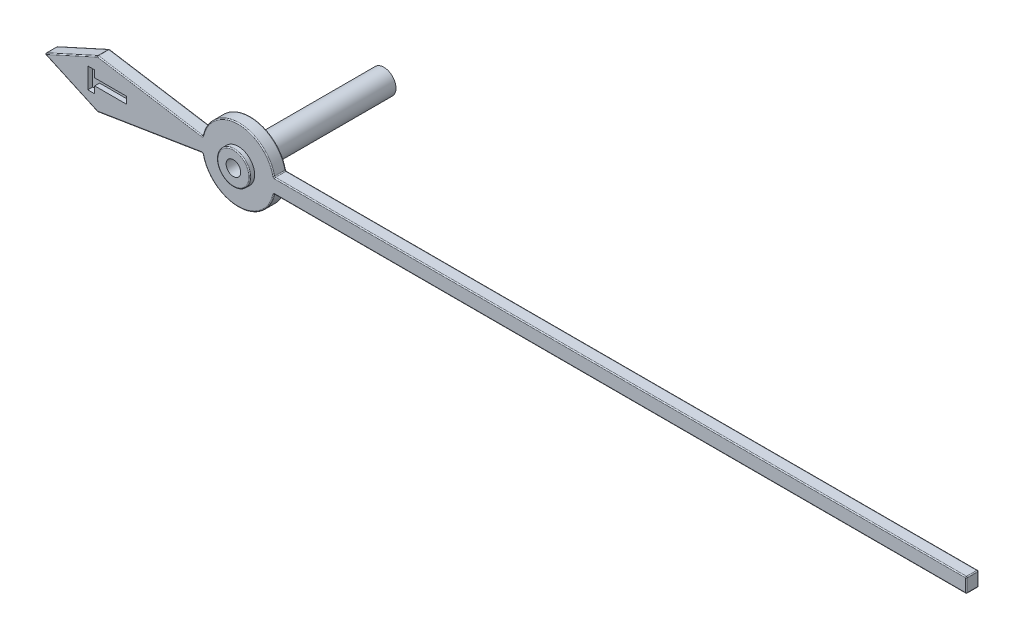
SolidWorks part; units mm, degrees
ref_plane "Front Plane" through (0, 0, 0) normal (0, 0, 1) x (1, 0, 0)
ref_plane "Top Plane" through (0, 0, 0) normal (0, 1, 0) x (1, 0, 0)
ref_plane "Right Plane" through (0, 0, 0) normal (1, 0, 0) x (0, 0, -1)
sketch "Sketch1" plane through (0, 0, 0) normal (0, 0, 1) x (1, 0, 0)
  line L0 (15, 0.15) -> (15, -0.15)
  line L1 (55, 0) -> (-55, 0) construction
  line L2 (0, -55) -> (0, 55) construction
  line L3 (0.7348, -0.15) -> (15, -0.15)
  line L4 (0.7348, 0.15) -> (15, 0.15)
  line L6 (-4, 0) -> (-2.9, 0.5)
  line L7 (-2.9, 0.5) -> (-0.7348, 0.15)
  line L8 (-4, 0) -> (-2.9, -0.5)
  line L9 (-2.9, -0.5) -> (-0.7348, -0.15)
  arc A0 (-0.7348, -0.15) -> (0.7348, -0.15) centre (0, 0) ccw
  circle A1 centre (0, 0) radius 0.25
  arc A2 (0.7348, 0.15) -> (-0.7348, 0.15) centre (0, 0) ccw
  dimension "D3" = 1.5
  dimension "D4" = 0.5
  dimension "D2" = 4
  dimension "D8" = 1
extrude "Boss-Extrude1" add sketch "Sketch1" along normal blind 0.25
fillet "Fillet1" radius 0.02 29 edges at (-2.9, -0.5, 0.125) (-0.7348, -0.15, 0.125) (0.7348, -0.15, 0.125) (15, -0.15, 0.125) (15, 0.15, 0.125) (0.7348, 0.15, 0.125) (-0.7348, 0.15, 0.125) (-2.9, 0.5, 0.125) (-4, 0, 0.125) (-3.45, 0.25, 0.25) (-1.8174, 0.325, 0.25) (0, 0.75, 0.25) (7.8674, 0.15, 0.25) (15, 0, 0.25) (7.8674, -0.15, 0.25) (0, -0.75, 0.25) (-1.8174, -0.325, 0.25) (-3.45, -0.25, 0.25) (-3.45, 0.25, 0) (-1.8174, 0.325, 0) (0, 0.75, 0) (7.8674, 0.15, 0) (15, 0, 0) (7.8674, -0.15, 0) (0, -0.75, 0) (-1.8174, -0.325, 0) (-3.45, -0.25, 0) (0.25, 0, 0.25) (0.25, 0, 0)
sketch "Sketch2" plane through (0, 0, 0.25) normal (0, 0, 1) x (1, 0, 0)
  text T0 "<b><r90>T</r></b>" font "Century Gothic" height in points 3
extrude "Cut-Extrude1" cut sketch "Sketch2" against normal blind 0.1
sketch "Sketch3" plane through (0, 0, 0.25) normal (0, 0, 1) x (1, 0, 0)
  circle A0 centre (0, 0) radius 0.3385
extrude "Boss-Extrude2" add sketch "Sketch3" along normal blind 0.1
sketch "Sketch4" plane through (0, 0, 0.25) normal (0, 0, -1) x (-1, 0, 0)
  circle A0 centre (0, 0) radius 0.25
  dimension "D1" = 0.5
extrude "Boss-Extrude3" add sketch "Sketch4" along normal blind 3
fillet "Fillet2" radius 0.02 1 edges at (0.3385, 0, 0.35)
sketch "Sketch5" plane through (0, 0, 0.35) normal (0, 0, 1) x (1, 0, 0)
  circle A0 centre (0, 0) radius 0.15
  dimension "D1" = 0.3
extrude "Cut-Extrude2" cut sketch "Sketch5" against normal blind 0.5
